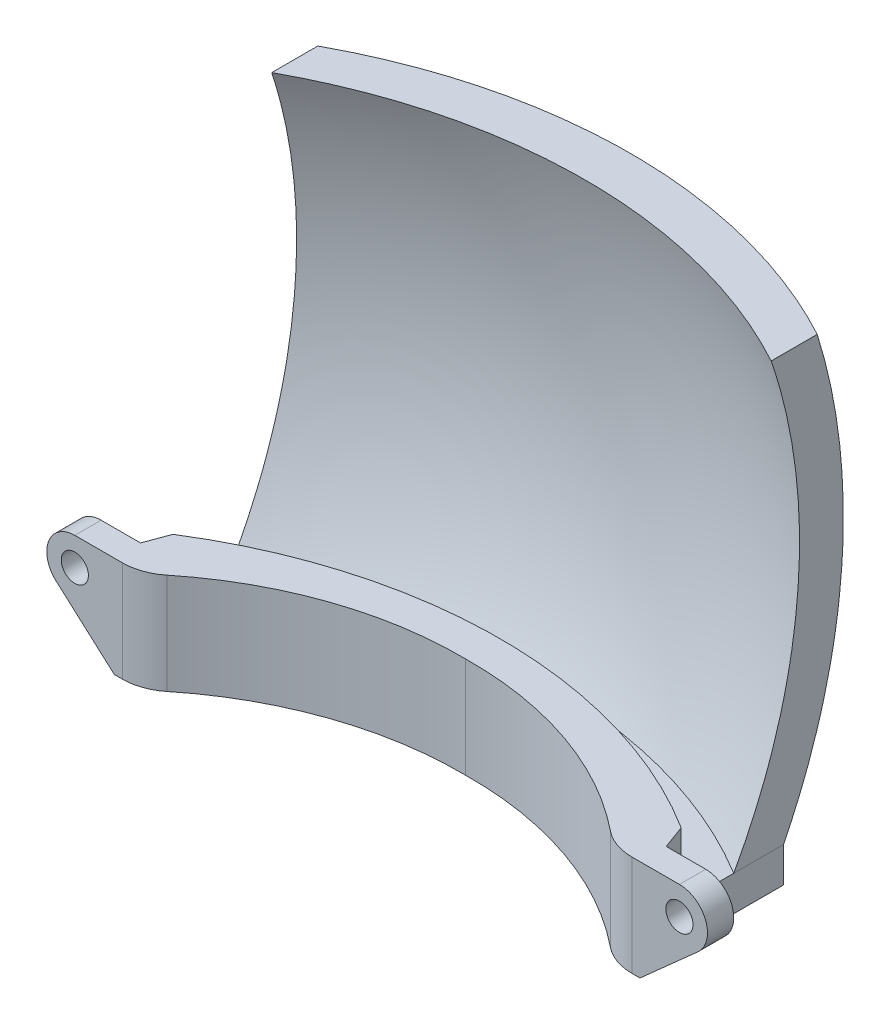
SolidWorks part; units mm, degrees
ref_plane "Front Plane" through (0, 0, 0) normal (0, 0, 1) x (1, 0, 0)
ref_plane "Top Plane" through (0, 0, 0) normal (0, 1, 0) x (1, 0, 0)
ref_plane "Right Plane" through (0, 0, 0) normal (1, 0, 0) x (0, 0, -1)
sketch "Sketch13" plane through (0, 0, 0) normal (1, 0, 0) x (0, 0, -1)
  line L2 (-33.5, 5) -> (25, 5) construction
  arc A1 (-15.698, 60.7256) -> (-15.698, -50.7256) centre (-33.5, 5) cw construction
  point P0 (-33.5, 0)
  point P4 (0, 0)
  point P10 (25, 5)
  dimension "D2" = 58.5
  dimension "D4" = 25
  dimension "D1" = 5
ref_plane "Plane4" through (0, 5, 0) normal (0, 1, 0) x (1, 0, 0)
sketch "Sketch15" plane through (0, 5, 0) normal (0, 1, 0) x (1, 0, 0)
  line L1 (-29, 25.2996) -> (-29, 30.2996)
  line L2 (29, 25.2996) -> (29, 30.2996)
  line L3 (-1000, -33.5) -> (49000, -33.5) construction
  arc A0 (-29, 25.2996) -> (29, 25.2996) centre (0, -29.5) cw
  arc A1 (-29, 30.2996) -> (29, 30.2996) centre (0, -24.5) cw
  point P4 (0, 32.5)
  point P11 (0, 37.5)
  dimension "D1" = 62
  dimension "D3" = 66
  dimension "D2" = 58
  dimension "D4" = 5
revolve "Revolve4" add sketch "Sketch15" angle 100 mid plane about L3
ref_plane "Plane2" through (0, 0, -44.9533) normal (0, 0, 1) x (1, 0, 0)
sketch "Sketch4" plane through (0, 0, -44.9533) normal (0, 0, 1) x (1, 0, 0)
  line L1 (28.5, 24) -> (-28.5, 24)
  line L2 (29, 24) -> (29, 68.9806)
  line L3 (29, 68.9806) -> (-29, 68.9806)
  line L4 (-29, 24) -> (-29, 68.9806)
  line L7 (29, 0) -> (-29, 0) construction
  line L12 (29, -43.8734) -> (29, 53.8734) construction
  line L13 (-29, 53.8734) -> (-29, -43.8734) construction
  line L14 (16.0862, 0) -> (-16.0862, 0) construction
  line L15 (-29, -24) -> (-29, -68.9806)
  line L16 (29, -68.9806) -> (-29, -68.9806)
  line L17 (29, -24) -> (29, -68.9806)
  line L18 (29, -24) -> (-29, -24)
  line L19 (29, -24) -> (28.5, 24)
  line L20 (29, 24) -> (29, -24)
  line L21 (0, 0) -> (0, 24) construction
  line L22 (-29, 24) -> (-29, -24)
  line L23 (-29, -24) -> (-28.5, 24)
  dimension "D1" = 24
  dimension "D2" = 57
extrude "Cut-Extrude3" cut sketch "Sketch4" along normal through all contours L22 L23 L1 L19 L20 L2 L3 L4 | L17 L18 L15 L16
sketch "Sketch5" plane through (0, -24, 0) normal (0, -1, 0) x (1, 0, 0)
  line L0 (-29.5, -17.6507) -> (29.5, -17.6507) construction
  line L1 (-1005.9323, -11.6507) -> (48994.0677, -11.6507) construction
  line L2 (-29, -17.6507) -> (-29, -23.3278)
  line L3 (29, -17.6507) -> (29, -23.3278)
  line L6 (-29, -17.6507) -> (-29, -11.6507)
  line L8 (-1024.6523, -8.9507) -> (48975.3477, -8.9507) construction
  line L9 (-29, -11.6507) -> (-30, -8.9507)
  line L10 (0, -1000) -> (0, 49000) construction
  line L11 (-30, -8.9507) -> (-38, -8.9507)
  line L12 (-38, -8.9507) -> (-38, -5.9507)
  line L13 (-1034.5956, -5.9507) -> (48965.4044, -5.9507) construction
  line L14 (-38, -5.9507) -> (-29.0694, -5.9507)
  line L15 (38, -5.9507) -> (29.0694, -5.9507)
  line L16 (38, -8.9507) -> (38, -5.9507)
  line L17 (30, -8.9507) -> (38, -8.9507)
  line L18 (29, -11.6507) -> (30, -8.9507)
  line L19 (29, -17.6507) -> (29, -11.6507)
  arc A0 (-29, -11.6507) -> (29, -11.6507) centre (0, 34.4931) ccw construction
  arc A1 (-30, -2.8062) -> (29, -2.8062) centre (-0.5, 23.4617) ccw construction
  arc A2 (-25.302, -7.281) -> (0, -16.0351) centre (-0.5, 23.4617) ccw
  arc A3 (-29.0694, -5.9507) -> (-25.302, -7.281) centre (-29.0694, -11.9507) cw
  arc A4 (25.302, -7.281) -> (0, -16.0351) centre (0.5, 23.4617) cw
  arc A5 (29.0694, -5.9507) -> (25.302, -7.281) centre (29.0694, -11.9507) ccw
  spline S0 degree 3 poles (97.1867, 968.6776) (-88.6683, 332.2572) (-121.2676, 15.4876) (-21.0844, -27.2517) (-19.9043, -27.7095) (-17.5071, -28.5479) (-16.2885, -28.9289) (-12.5851, -29.95) (-10.0925, -30.4582) (-6.3188, -30.9679) (-5.055, -31.0956) (-2.5159, -31.2658) (-1.2381, -31.3083) (2.599, -31.3055) (5.1277, -31.1311) (10.1283, -30.451) (12.6004, -29.9453) (16.2655, -28.9355) (17.48, -28.5569) (19.8943, -27.7134) (21.0819, -27.2528) (147.9571, 26.879) (34.698, 511.4945) (-65.3099, 972.2112) knots -5.201414 -5.201414 -5.201414 -5.201414 0.125 0.125 0.1875 0.1875 0.25 0.25 0.375 0.375 0.4375 0.4375 0.5 0.5 0.625 0.625 0.75 0.75 0.8125 0.8125 0.875 0.875 7.612251 7.612251 7.612251 7.612251 only from (-29, -23.3278) to (29, -23.3278) construction
  spline S2 degree 3 poles (-29, -23.3278) (-26.8214, -24.6221) (-24.5701, -25.7647) (-21.0844, -27.2517) (-19.9043, -27.7095) (-17.5071, -28.5479) (-16.2885, -28.9289) (-12.5851, -29.95) (-10.0925, -30.4582) (-6.3188, -30.9679) (-5.055, -31.0956) (-2.5159, -31.2658) (-1.2381, -31.3083) (2.599, -31.3055) (5.1277, -31.1311) (10.1283, -30.451) (12.6004, -29.9453) (16.2655, -28.9355) (17.48, -28.5569) (19.8943, -27.7134) (21.0819, -27.2528) (24.5805, -25.7601) (26.8306, -24.6167) (29, -23.3278) knots 0 0 0 0 0.125 0.125 0.1875 0.1875 0.25 0.25 0.375 0.375 0.4375 0.4375 0.5 0.5 0.625 0.625 0.75 0.75 0.8125 0.8125 0.875 0.875 1 1 1 1
  point P3 (0, 0)
  point P25 (-0.5, -16.0383)
  point P26 (0, -20.0069)
  point P27 (0, 0)
  point P31 (-26.8659, -5.9507)
  point P33 (0, 0)
  point P34 (0, 0)
  point P42 (0, 0)
  point P43 (0, 0)
  point P44 (0, 0)
  point P45 (0, 0)
  point P46 (29, -28.2608)
  dimension "D3" = 54.5
  dimension "D5" = 39.5
  dimension "D9" = 6
  dimension "D2" = 6
  dimension "D4" = 2.7
  dimension "D6" = 4
  dimension "D7" = 8
  dimension "D8" = 3
  dimension "D10" = 1
extrude "Boss-Extrude1" add sketch "Sketch5" along normal blind 4
sketch "Sketch6" plane through (0, -24, 0) normal (0, 1, 0) x (1, 0, 0)
  line L5 (-29, 17.6507) -> (-29, 11.6507)
  line L6 (-29, 11.6507) -> (-30, 8.9507)
  line L15 (29.0694, 5.9507) -> (38, 5.9507)
  line L16 (38, 5.9507) -> (38, 8.9507)
  line L17 (38, 8.9507) -> (30, 8.9507)
  line L18 (30, 8.9507) -> (29, 11.6507)
  line L25 (29.0694, 5.9507) -> (38, 5.9507)
  line L26 (38, 5.9507) -> (38, 8.9507)
  line L27 (38, 8.9507) -> (30, 8.9507)
  line L28 (30, 8.9507) -> (29, 11.6507)
  line L33 (-29, 11.6507) -> (-30, 8.9507)
  line L35 (-30, 8.9507) -> (-38, 8.9507)
  line L37 (-30, 8.9507) -> (-38, 8.9507)
  line L38 (-38, 8.9507) -> (-38, 5.9507)
  line L39 (-38, 8.9507) -> (-38, 5.9507)
  line L40 (-38, 5.9507) -> (-29.0694, 5.9507)
  line L41 (-38, 5.9507) -> (-29.0694, 5.9507)
  line L42 (29, 11.6507) -> (29, 17.6507)
  line L43 (29, 11.6507) -> (29, 17.6507)
  arc A0 (-29, 11.6507) -> (29, 11.6507) centre (0, -34.4931) cw
  arc A5 (-29.0694, 5.9507) -> (-25.302, 7.281) centre (-29.0694, 11.9507) ccw
  arc A6 (25.302, 7.281) -> (0, 16.0351) centre (0.5, -23.4617) ccw
  arc A7 (25.302, 7.281) -> (29.0694, 5.9507) centre (29.0694, 11.9507) ccw
  arc A10 (25.302, 7.281) -> (0, 16.0351) centre (0.5, -23.4617) ccw
  arc A11 (25.302, 7.281) -> (29.0694, 5.9507) centre (29.0694, 11.9507) ccw
  arc A15 (-29.0694, 5.9507) -> (-25.302, 7.281) centre (-29.0694, 11.9507) ccw
  arc A17 (0, 16.0351) -> (-25.302, 7.281) centre (-0.5, -23.4617) ccw
  arc A18 (0, 16.0351) -> (-25.302, 7.281) centre (-0.5, -23.4617) ccw
  spline S1 degree 3 poles (-840.8337, -1763.1419) (102.3884, -463.1023) (136.0604, -28.34) (19.9143, 22.1683) (17.5328, 23.0176) (13.8653, 24.0492) (12.6269, 24.3525) (10.1174, 24.8758) (8.8568, 25.0936) (5.0635, 25.6155) (2.5147, 25.7896) (-2.6102, 25.7852) (-5.1426, 25.6071) (-10.1498, 24.9131) (-12.6246, 24.3973) (-16.293, 23.3667) (-17.5101, 22.9796) (-19.9222, 22.1197) (-21.1066, 21.6507) (-201.7796, -57.0726) (117.7807, -1035.4688) (391.3923, -1930.9864) knots -6.010686 -6.010686 -6.010686 -6.010686 0.125 0.125 0.25 0.25 0.3125 0.3125 0.375 0.375 0.5 0.5 0.625 0.625 0.75 0.75 0.8125 0.8125 0.875 0.875 10.518673 10.518673 10.518673 10.518673 only from (29, 17.6507) to (-29, 17.6507)
  spline S2 degree 3 poles (29, 17.6507) (26.8099, 18.983) (24.5522, 20.1514) (19.9143, 22.1683) (17.5328, 23.0176) (13.8653, 24.0492) (12.6269, 24.3525) (10.1174, 24.8758) (8.8568, 25.0936) (5.0635, 25.6155) (2.5147, 25.7896) (-2.6102, 25.7852) (-5.1426, 25.6071) (-10.1498, 24.9131) (-12.6246, 24.3973) (-16.293, 23.3667) (-17.5101, 22.9796) (-19.9222, 22.1197) (-21.1066, 21.6507) (-24.5968, 20.13) (-26.8397, 18.9649) (-29, 17.6507) knots 0 0 0 0 0.125 0.125 0.25 0.25 0.3125 0.3125 0.375 0.375 0.5 0.5 0.625 0.625 0.75 0.75 0.8125 0.8125 0.875 0.875 1 1 1 1
  point P5 (0, 0)
  point P6 (0, 0)
  point P7 (-29.0694, 9.5635)
  point P9 (29.0694, 9.8295)
  point P11 (29, 9.8295)
  line M19 (-29, 11.6507) -> (-30, 8.9507)
  line M20 (-30, 8.9507) -> (-38, 8.9507)
  line M21 (-38, 8.9507) -> (-38, 5.9507)
  line M22 (-38, 5.9507) -> (-29.0694, 5.9507)
  arc M23 (-29.0694, 5.9507) -> (-25.302, 7.281) centre (-29.0694, 11.9507) ccw
  arc M24 (-25.302, 7.281) -> (0, 16.0351) centre (-0.5, -23.4617) cw
  arc M25 (0, 16.0351) -> (25.302, 7.281) centre (0.5, -23.4617) cw
  arc M26 (25.302, 7.281) -> (29.0694, 5.9507) centre (29.0694, 11.9507) ccw
  line M27 (29.0694, 5.9507) -> (38, 5.9507)
  line M28 (38, 5.9507) -> (38, 8.9507)
  line M29 (38, 8.9507) -> (30, 8.9507)
  line M30 (30, 8.9507) -> (29, 11.6507)
  dimension "D2" = 54.5
  dimension "D1" = 0
extrude "Boss-Extrude2" add sketch "Sketch6" along normal blind 7.5 contours A0 M19 M20 M21 M22 M23 M24 M25 M26 M27 M28 M29 M30
sketch "Sketch7" plane through (0, 0, -5.9507) normal (0, 0, 1) x (1, 0, 0)
  line L1 (-38, -24) -> (-29.0694, -24) construction
  line L2 (-38, -28) -> (-38, -16.5) construction
  line L3 (-29.0694, -28) -> (-29.0694, -16.5) construction
  line L4 (0, -1000) -> (0, 49000) construction
  circle A0 centre (-34.5, -19.7) radius 1.55
  circle A1 centre (34.5, -19.7) radius 1.55
  dimension "D1" = 3.1
  dimension "D2" = 4.3
  dimension "D3" = 34.5
extrude "Cut-Extrude4" cut sketch "Sketch7" against normal up to next
sketch "Sketch8" plane through (0, 0, -5.9507) normal (0, 0, 1) x (1, 0, 0)
  line L0 (0, -1000) -> (0, 49000) construction
  line L1 (-38, -16.5) -> (-29.0694, -16.5) construction
  line L2 (-34.5, -16.5) -> (-34.5, -22.9) construction
  line L4 (-30, -28) -> (-30, -16.5) construction
  line L5 (-29.0694, -28) -> (-38, -28) construction
  line L6 (-30, -28) -> (-36.6297, -22.0884)
  line L7 (-34.5, -16.5) -> (-38, -16.5)
  line L8 (-38, -16.5) -> (-38, -28)
  line L9 (-38, -28) -> (-30, -28)
  line L10 (38, -16.5) -> (38, -28)
  line L11 (34.5, -16.5) -> (38, -16.5)
  line L12 (30, -28) -> (36.6297, -22.0884)
  line L13 (38, -28) -> (30, -28)
  arc A0 (-34.5, -16.5) -> (-36.6297, -22.0884) centre (-34.5, -19.7) ccw
  arc A4 (34.5, -16.5) -> (36.6297, -22.0884) centre (34.5, -19.7) cw
  point P6 (0, 0)
  point P8 (-38, -17.1343)
  point P13 (0, 0)
  point P27 (-30, -17.9118)
extrude "Cut-Extrude5" cut sketch "Sketch8" against normal up to next
equation "\"plane_offset\" = 5"
equation "\"D1@Sketch13\"=\"plane_offset\""
